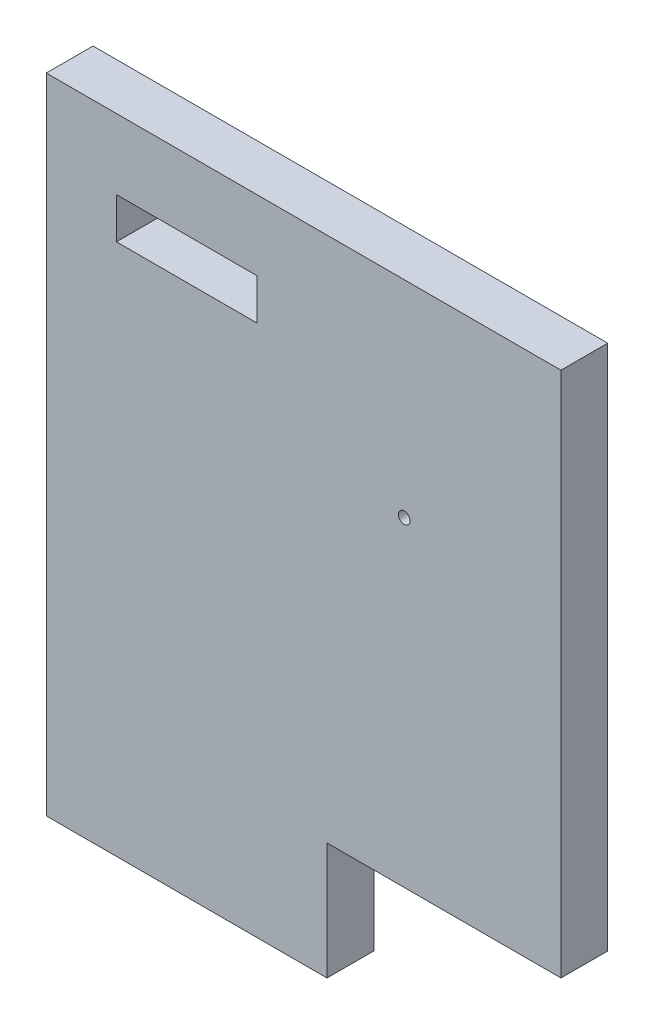
SolidWorks part; units mm, degrees
ref_plane "Ebene vorne" through (0, 0, 0) normal (0, 0, 1) x (1, 0, 0)
ref_plane "Ebene oben" through (0, 0, 0) normal (0, 1, 0) x (1, 0, 0)
ref_plane "Ebene rechts" through (0, 0, 0) normal (1, 0, 0) x (0, 0, -1)
sketch "Skizze1" plane through (0, 0, 0) normal (0, 0, 1) x (1, 0, 0)
  line L0 (12, 0) -> (12, 76.3542) construction
  line L1 (0, 0) -> (24, 0)
  line L2 (0, 0) -> (0, 55)
  line L3 (0, 55) -> (24, 55)
  line L4 (24, 0) -> (24, 55)
  line L5 (6, 49) -> (18, 49)
  line L6 (6, 49) -> (6, 45.5)
  line L7 (6, 45.5) -> (18, 45.5)
  line L8 (18, 49) -> (18, 45.5)
  dimension "D1" = 24
  dimension "D2" = 55
  dimension "D3" = 12
  dimension "D4" = 6
  dimension "D5" = 3.5
extrude "Aufsatz-Linear austragen1" add sketch "Skizze1" along normal blind 4
sketch "Skizze3" plane through (0, 0, 4) normal (0, 0, 1) x (1, 0, 0)
  line L0 (24, 55) -> (44, 55)
  line L1 (24, 0) -> (24, 55) construction
  line L2 (44, 55) -> (44, 10)
  line L3 (44, 10) -> (24, 10)
  line L4 (24, 10) -> (24, 55)
  line L5 (24, 55) -> (0, 55) construction
  dimension "D1" = 45
  dimension "D2" = 20
  dimension "D3" = 0
extrude "Aufsatz-Linear austragen3" add sketch "Skizze3" against normal up to surface (4 mm away) up to face at (12, 27.5, 0)
sketch "Skizze4" plane through (0, 0, 4) normal (0, 0, 1) x (1, 0, 0)
  circle A0 centre (30.6, 37.3776) radius 0.5
  dimension "D1" = 1
extrude "Schnitt-Linear austragen1" cut sketch "Skizze4" against normal up to next contours A0
